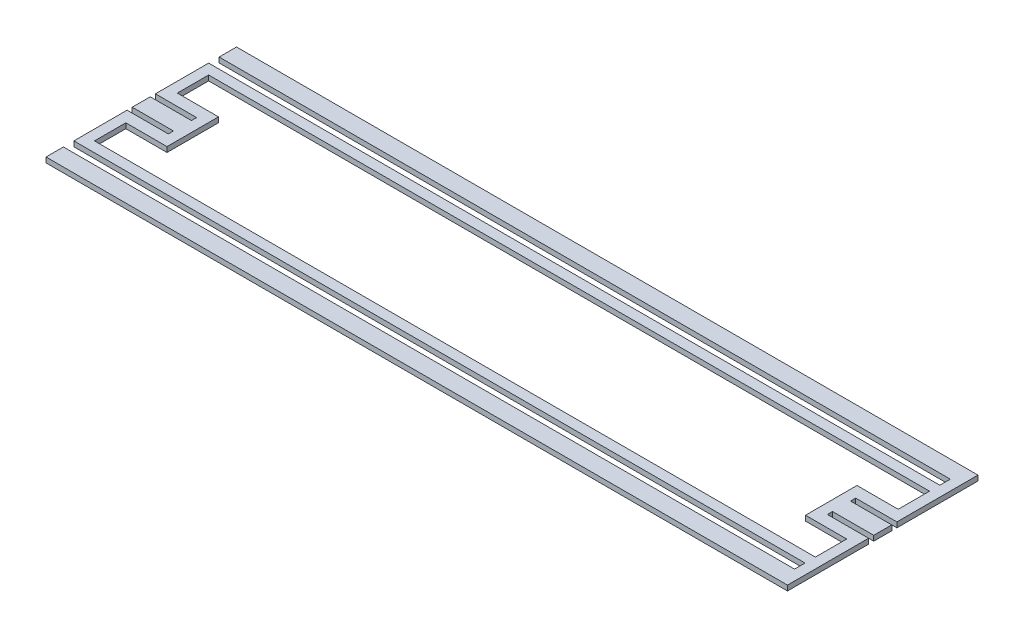
SolidWorks part; units mm, degrees
ref_plane "Front Plane" through (0, 0, 0) normal (0, 0, 1) x (1, 0, 0)
ref_plane "Top Plane" through (0, 0, 0) normal (0, 1, 0) x (1, 0, 0)
ref_plane "Right Plane" through (0, 0, 0) normal (1, 0, 0) x (0, 0, -1)
sketch "Sketch1" plane through (0, 0, 0) normal (0, 1, 0) x (1, 0, 0)
  line L0 (-228.6, 41.5449) -> (-228.6, 8.7313)
  line L1 (-228.6, 58.7375) -> (228.6, 58.7375)
  line L2 (-228.6, 58.7375) -> (-228.6, 48.0219)
  line L3 (-228.6, -58.7375) -> (228.6, -58.7375)
  line L4 (228.6, 58.7375) -> (228.6, 8.7313)
  line L5 (-228.6, 58.7375) -> (228.6, -58.7375) construction
  line L6 (-228.6, -58.7375) -> (228.6, 58.7375) construction
  line L7 (-228.6, -58.7375) -> (190.5, -58.7375)
  line L8 (-228.6, -58.7375) -> (-228.6, -48.0219)
  line L9 (-228.6, -48.0219) -> (222.25, -48.0219)
  line L11 (-228.6, 58.7375) -> (190.5, 58.7375)
  line L12 (-228.6, 58.7375) -> (-228.6, 48.0219)
  line L13 (-228.6, 48.0219) -> (222.25, 48.0219)
  line L15 (-228.6, -48.0219) -> (222.25, -48.0219)
  line L17 (-228.6, -41.5449) -> (222.25, -41.5449)
  line L18 (222.25, -48.0219) -> (222.25, -41.5449)
  line L19 (-228.6, 48.0219) -> (222.25, 48.0219)
  line L21 (-228.6, 41.5449) -> (222.25, 41.5449)
  line L22 (222.25, 48.0219) -> (222.25, 41.5449)
  line L23 (-228.6, -48.0219) -> (-228.6, -58.7375)
  line L24 (222.25, 15.875) -> (196.85, 15.875)
  line L25 (-222.25, -35.1949) -> (222.25, -35.1949)
  line L26 (-222.25, -35.1949) -> (-222.25, -15.875)
  line L27 (-222.25, 35.1949) -> (222.25, 35.1949)
  line L28 (222.25, -35.1949) -> (222.25, -15.875)
  line L29 (-222.25, -35.1949) -> (222.25, 35.1949) construction
  line L30 (-222.25, 35.1949) -> (222.25, -35.1949) construction
  line L31 (196.85, 15.875) -> (196.85, -15.875)
  line L32 (196.85, -15.875) -> (222.25, -15.875)
  line L33 (222.25, 8.7313) -> (203.2, 8.7313)
  line L34 (203.2, 8.7313) -> (203.2, 5.5563)
  line L35 (203.2, 5.5563) -> (222.25, 5.5562)
  line L36 (222.25, -5.5562) -> (203.2, -5.5563)
  line L37 (203.2, -5.5563) -> (203.2, -8.7312)
  line L38 (203.2, -8.7312) -> (222.25, -8.7312)
  line L39 (203.2, 5.5563) -> (203.2, -5.5563) construction
  line L40 (222.25, 8.7313) -> (228.6, 8.7313)
  line L41 (222.25, 5.5562) -> (228.6, 5.5562)
  line L42 (222.25, -8.7312) -> (228.6, -8.7312)
  line L43 (222.25, -5.5562) -> (228.6, -5.5562)
  line L44 (222.25, -5.5562) -> (222.25, 5.5562) construction
  line L45 (222.25, 5.5562) -> (222.25, 8.7313) construction
  line L46 (222.25, 8.7313) -> (222.25, 15.875) construction
  line L47 (222.25, 15.875) -> (222.25, 35.1949)
  line L48 (222.25, -15.875) -> (222.25, -8.7312) construction
  line L49 (222.25, -8.7312) -> (222.25, -5.5562) construction
  line L50 (228.6, -5.5562) -> (228.6, -8.7312) construction
  line L51 (228.6, -8.7312) -> (228.6, -58.7375)
  line L52 (228.6, 8.7313) -> (228.6, 5.5562) construction
  line L53 (228.6, 5.5562) -> (228.6, -5.5562)
  line L54 (0, 35.1949) -> (0, -35.1949) construction
  line L55 (-222.25, 8.7313) -> (-228.6, 8.7313)
  line L56 (-222.25, 5.5562) -> (-228.6, 5.5562)
  line L57 (-222.25, -5.5562) -> (-228.6, -5.5562)
  line L58 (-222.25, -8.7312) -> (-228.6, -8.7312)
  line L59 (-196.85, -15.875) -> (-222.25, -15.875)
  line L60 (-203.2, 8.7313) -> (-203.2, 5.5563)
  line L61 (-203.2, -5.5563) -> (-203.2, -8.7312)
  line L62 (-203.2, -8.7312) -> (-222.25, -8.7312)
  line L63 (-222.25, -5.5562) -> (-203.2, -5.5563)
  line L64 (-203.2, 5.5563) -> (-222.25, 5.5562)
  line L65 (-222.25, 8.7313) -> (-203.2, 8.7313)
  line L66 (-196.85, 15.875) -> (-196.85, -15.875)
  line L67 (-222.25, 15.875) -> (-196.85, 15.875)
  line L68 (-228.6, 5.5562) -> (-228.6, -5.5562)
  line L69 (-222.25, 15.875) -> (-222.25, 35.1949)
  line L71 (-228.6, -8.7312) -> (-228.6, -41.5449)
  point P0 (0, 0)
  point P16 (0, 0)
  point P26 (196.85, 0)
  point P35 (203.2, 0)
  point P36 (-196.85, 0)
  point P43 (0, 35.1949)
  dimension "D1" = 457.2
  dimension "D2" = 117.475
  dimension "D4" = 10.7156
  dimension "D5" = 10.7156
  dimension "D6" = 6.477
  dimension "D7" = 6.477
  dimension "D3" = 6.35
  dimension "D8" = 6.35
  dimension "D9" = 6.35
  dimension "D10" = 6.35
  dimension "D11" = 25.4
  dimension "D12" = 31.75
  dimension "D13" = 3.175
  dimension "D14" = 3.175
  dimension "D15" = 17.4625
  dimension "D16" = 19.05
extrude "Boss-Extrude1" add sketch "Sketch1" along normal mid plane 3.175
equation "\"D1@Sketch1\"=18in"
equation "\"D6@Sketch1\"=\"D7@Sketch1\""
